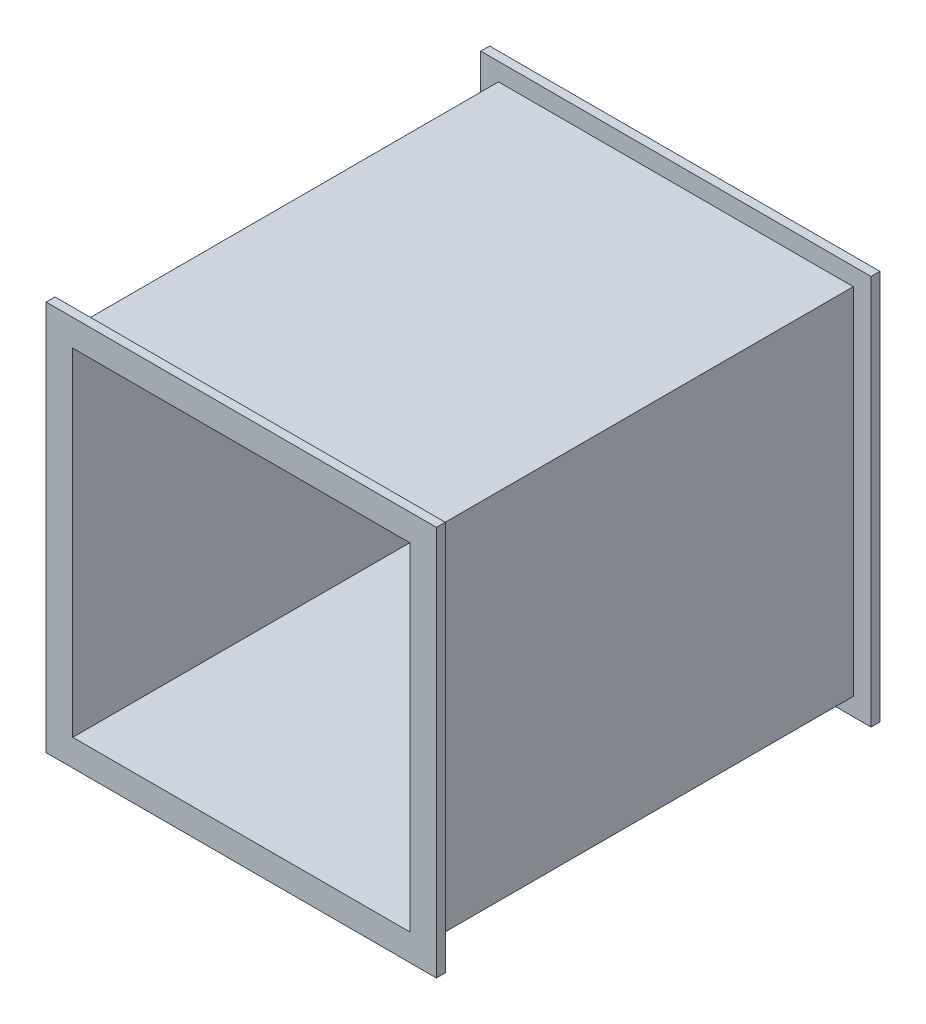
SolidWorks part; units mm, degrees
ref_plane "Front Plane" through (0, 0, 0) normal (0, 0, 1) x (1, 0, 0)
ref_plane "Top Plane" through (0, 0, 0) normal (0, 1, 0) x (1, 0, 0)
ref_plane "Right Plane" through (0, 0, 0) normal (1, 0, 0) x (0, 0, -1)
sketch "Sketch1" plane through (0, 0, 0) normal (0, 0, 1) x (1, 0, 0)
  line L1 (-100, 100) -> (100, 100)
  line L2 (-100, 100) -> (-100, -100)
  line L3 (-100, -100) -> (100, -100)
  line L4 (100, 100) -> (100, -100)
  line L5 (-100, 100) -> (100, -100) construction
  line L6 (-100, -100) -> (100, 100) construction
  point P0 (0, 0)
  dimension "D1" = 200
  dimension "D2" = 200
extrude "Boss-Extrude1" add sketch "Sketch1" along normal blind 250
sketch "Sketch2" plane through (0, 0, 250) normal (0, 0, 1) x (1, 0, 0)
  line L8 (110, -110) -> (110, 110)
  line L9 (110, 110) -> (-110, 110)
  line L10 (-110, 110) -> (-110, -110)
  line L11 (-110, -110) -> (110, -110)
  line L12 (110, -110) -> (110, 110)
  line L13 (110, 110) -> (-110, 110)
  line L14 (-110, 110) -> (-110, -110)
  line L15 (-110, -110) -> (110, -110)
  dimension "D1" = 10
extrude "Boss-Extrude3" add sketch "Sketch2" against normal blind 5 contours L13 L14 L15 L12
sketch "Sketch3" plane through (0, 0, 0) normal (0, 0, -1) x (-1, 0, 0)
  line L8 (-110, 110) -> (-110, -110)
  line L9 (-110, -110) -> (110, -110)
  line L10 (110, -110) -> (110, 110)
  line L11 (110, 110) -> (-110, 110)
  line L12 (-110, 110) -> (-110, -110)
  line L13 (-110, -110) -> (110, -110)
  line L14 (110, -110) -> (110, 110)
  line L15 (110, 110) -> (-110, 110)
  dimension "D1" = 10
extrude "Boss-Extrude4" add sketch "Sketch3" against normal blind 5
sketch "Sketch4" plane through (0, 0, 250) normal (0, 0, 1) x (1, 0, 0)
  line L1 (-95, -95) -> (95, -95)
  line L2 (-95, -95) -> (-95, 95)
  line L3 (-95, 95) -> (95, 95)
  line L4 (95, -95) -> (95, 95)
  line L5 (-95, -95) -> (95, 95) construction
  line L6 (-95, 95) -> (95, -95) construction
  point P0 (0, 0)
  dimension "D1" = 190
  dimension "D2" = 190
extrude "Cut-Extrude1" cut sketch "Sketch4" against normal through all
